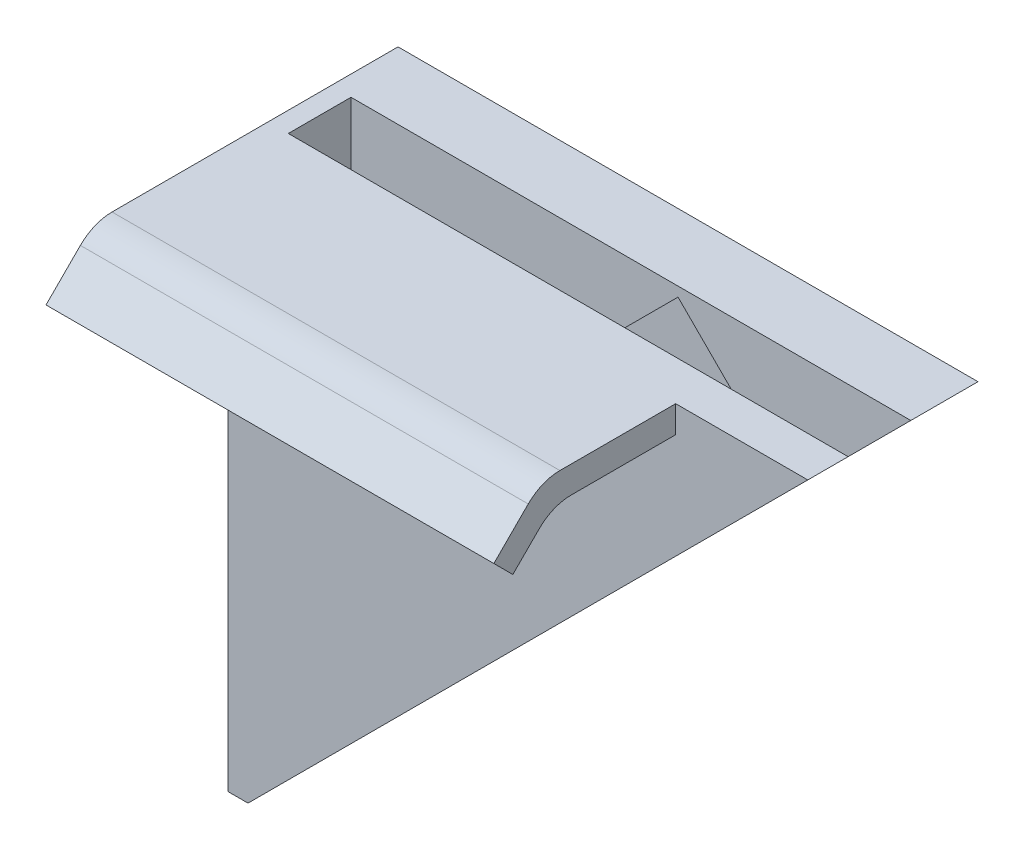
SolidWorks part; units mm, degrees
ref_plane "Alzado" through (0, 0, 0) normal (0, 0, 1) x (1, 0, 0)
ref_plane "Planta" through (0, 0, 0) normal (0, 1, 0) x (1, 0, 0)
ref_plane "Vista lateral" through (0, 0, 0) normal (1, 0, 0) x (0, 0, -1)
sketch "Croquis1" plane through (0, 0, 0) normal (0, 0, 1) x (1, 0, 0)
  line L0 (0, 0) -> (25, 0)
  line L1 (0, 0) -> (0, -25)
  line L2 (0, -25) -> (25, 0)
  dimension "D1" = 25
extrude "Saliente-Extruir1" add sketch "Croquis1" along normal blind 1.8
sketch "Croquis2" plane through (0, 0, 0) normal (-1, 0, 0) x (0, 0, 1)
  line L1 (1.8, 0) -> (-5.8, 0)
  line L2 (1.8, 0) -> (1.8, -25)
  line L3 (1.8, -25) -> (-5.8, -25)
  line L4 (-5.8, 0) -> (-5.8, -25)
  dimension "D1" = 7.6
extrude "Saliente-Extruir2" add sketch "Croquis2" along normal blind 0.9
sketch "Croquis3" plane through (0, 0, -5.8) normal (0, 0, -1) x (-1, 0, 0)
  line L0 (0, 0) -> (-25, 0)
  line L1 (-25, 0) -> (0, -25)
  line L2 (0, -25) -> (0, 0)
  line L3 (-25, 0) -> (0, 0) construction
extrude "Saliente-Extruir3" add sketch "Croquis3" against normal blind 3
sketch "Croquis4" plane through (0, 0, -2.8) normal (0, 0, 1) x (1, 0, 0)
  line L0 (18.8816, -4.7041) -> (4.7041, -18.8816)
  line L1 (12.5, -12.5) -> (11.7929, -11.7929) construction
  line L2 (25, 0) -> (0, -25) construction
  line L3 (4.7041, -18.8816) -> (0.4262, -14.6036)
  line L4 (0.4262, -14.6036) -> (14.6036, -0.4262)
  line L5 (14.6036, -0.4262) -> (18.8816, -4.7041)
  point P6 (11.7929, -11.7929)
  dimension "D1" = 20.05
  dimension "D2" = 1
  dimension "D3" = 6.05
extrude "Cortar-Extruir1" cut sketch "Croquis4" against normal blind 2.05
sketch "Croquis5" plane through (-0.9, 0, 0) normal (-1, 0, 0) x (0, 0, 1)
  line L0 (1.8, 0) -> (7.8, 0)
  line L1 (1.8, -25) -> (1.8, 0) construction
  line L2 (7.8, 0) -> (9.9213, -2.1213)
  line L3 (9.9213, -2.1213) -> (9.0728, -2.9698)
  line L4 (9.0728, -2.9698) -> (7.3029, -1.2)
  line L5 (7.3029, -1.2) -> (1.8, -1.2)
  line L6 (1.8, -1.2) -> (1.8, 0)
  dimension "D1" = 6
  dimension "D2" = 0
  dimension "D3" = 3
  dimension "D4" = 135
  dimension "D5" = 1.2
  dimension "D6" = 1.2
extrude "Saliente-Extruir4" add sketch "Croquis5" against normal blind 20
fillet "Redondeo1" radius 2 2 edges at (9.1, -1.2, 7.3029) (9.1, 0, 7.8)
